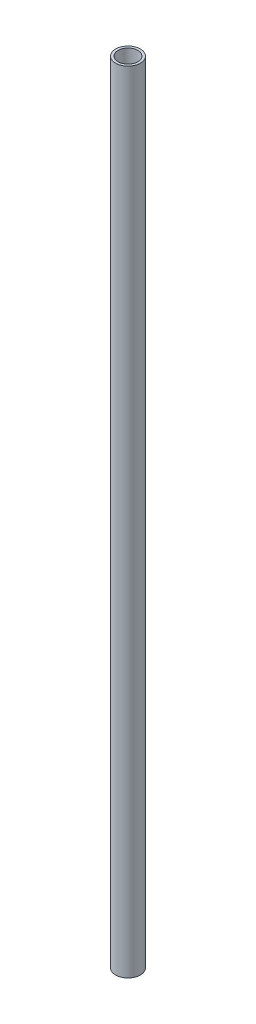
SolidWorks part; units mm, degrees
ref_plane "Front Plane" through (0, 0, 0) normal (0, 0, 1) x (1, 0, 0)
ref_plane "Top Plane" through (0, 0, 0) normal (0, 1, 0) x (1, 0, 0)
ref_plane "Right Plane" through (0, 0, 0) normal (1, 0, 0) x (0, 0, -1)
sketch "Sketch1" plane through (0, 0, 0) normal (0, 1, 0) x (1, 0, 0)
  circle A0 centre (0, 0) radius 7.9375
  circle A1 centre (0, 0) radius 6.35
  dimension "D1" = 15.875
  dimension "D2" = 12.7
extrude "Boss-Extrude1" add sketch "Sketch1" along normal blind 508
